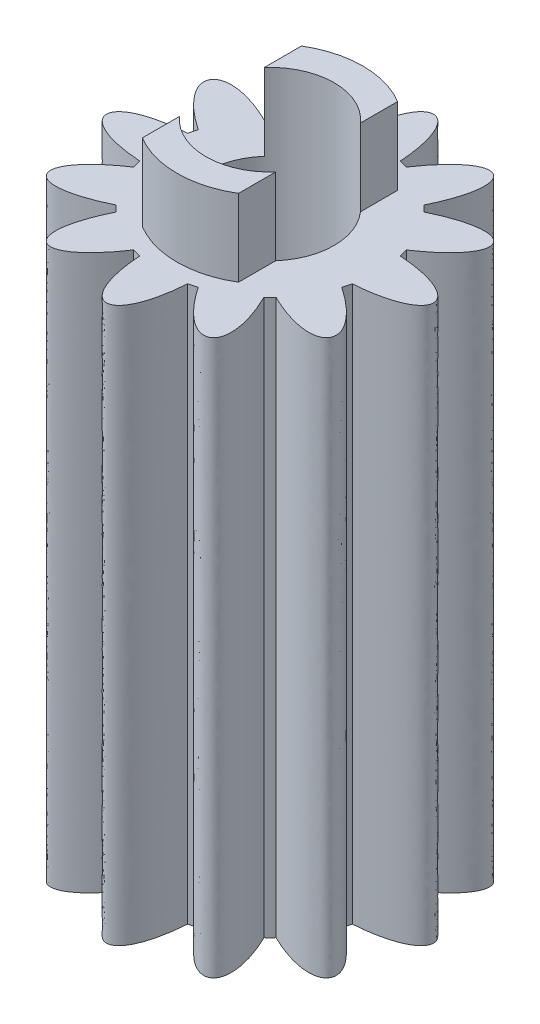
SolidWorks part; units mm, degrees
ref_plane "Front Plane" through (0, 0, 0) normal (0, 0, 1) x (1, 0, 0)
ref_plane "Top Plane" through (0, 0, 0) normal (0, 1, 0) x (1, 0, 0)
ref_plane "Right Plane" through (0, 0, 0) normal (1, 0, 0) x (0, 0, -1)
sketch "Sketch1" plane through (0, 0, 0) normal (0, 1, 0) x (1, 0, 0)
  line L0 (0, 0.0596) -> (0, 50000.0596) construction
  line L1 (0.75, -3.3162) -> (-0.75, -3.3162) construction
  line L2 (0.75, -3.3162) -> (0.75, 3.3162) construction
  line L3 (0.75, 3.3162) -> (-0.75, 3.3162) construction
  line L4 (-0.75, -3.3162) -> (-0.75, 3.3162) construction
  line L5 (0.75, -3.3162) -> (-0.75, 3.3162) construction
  line L6 (0.75, 3.3162) -> (-0.75, -3.3162) construction
  line L7 (0, 0) -> (0.75, 3.3162) construction
  circle A0 centre (0, 0) radius 3.4
  circle A1 centre (0, 0) radius 5.1 construction
  spline S0 degree 3 poles (-0.75, 3.3162) (-0.5833, 5.6946) (0.5833, 5.6946) (0.75, 3.3162) knots 0 0 0 0 1 1 1 1
  spline S1 degree 3 poles (1.0086, 3.247) (2.3421, 5.2233) (3.3525, 4.64) (2.3076, 2.497) knots 0 0 0 0 1 1 1 1
  spline S2 degree 3 poles (2.497, 2.3076) (4.64, 3.3525) (5.2233, 2.3421) (3.247, 1.0086) knots 0 0 0 0 1 1 1 1
  spline S3 degree 3 poles (3.3162, 0.75) (5.6946, 0.5833) (5.6946, -0.5833) (3.3162, -0.75) knots 0 0 0 0 1 1 1 1
  spline S4 degree 3 poles (3.247, -1.0086) (5.2233, -2.3421) (4.64, -3.3525) (2.497, -2.3076) knots 0 0 0 0 1 1 1 1
  spline S5 degree 3 poles (2.3076, -2.497) (3.3525, -4.64) (2.3421, -5.2233) (1.0086, -3.247) knots 0 0 0 0 1 1 1 1
  spline S6 degree 3 poles (0.75, -3.3162) (0.5833, -5.6946) (-0.5833, -5.6946) (-0.75, -3.3162) knots 0 0 0 0 1 1 1 1
  spline S7 degree 3 poles (-1.0086, -3.247) (-2.3421, -5.2233) (-3.3525, -4.64) (-2.3076, -2.497) knots 0 0 0 0 1 1 1 1
  spline S8 degree 3 poles (-2.497, -2.3076) (-4.64, -3.3525) (-5.2233, -2.3421) (-3.247, -1.0086) knots 0 0 0 0 1 1 1 1
  spline S9 degree 3 poles (-3.3162, -0.75) (-5.6946, -0.5833) (-5.6946, 0.5833) (-3.3162, 0.75) knots 0 0 0 0 1 1 1 1
  spline S10 degree 3 poles (-3.247, 1.0086) (-5.2233, 2.3421) (-4.64, 3.3525) (-2.497, 2.3076) knots 0 0 0 0 1 1 1 1
  spline S11 degree 3 poles (-2.3076, 2.497) (-3.3525, 4.64) (-2.3421, 5.2233) (-1.0086, 3.247) knots 0 0 0 0 1 1 1 1
  point P12 (0, 0)
  point P13 (0, 0)
  point P48 (0, 0)
  point P49 (0, 0)
  dimension "D1" = 6.8
  dimension "D2" = 10.2
  dimension "D3" = 1.5
  dimension "D4" = 3.4
extrude "Boss-Extrude1" add sketch "Sketch1" along normal blind 17.3 contours A0 | S9 A0 | S8 A0 | S7 A0 | S6 A0 | S5 A0 | S4 A0 | S3 A0 | S2 A0 | S1 A0 | S10 A0 | S11 A0 | S0 A0
sketch "Sketch4" plane through (0, 17.3, 0) normal (0, 1, 0) x (1, 0, 0)
  circle A0 centre (0, 0) radius 2.9
  dimension "D1" = 5.8
extrude "Boss-Extrude2" add sketch "Sketch4" along normal blind 2.4
sketch "Sketch2" plane through (0, 0, 0) normal (0, -1, 0) x (1, 0, 0)
  circle A0 centre (0, 0) radius 2
  dimension "D1" = 4
extrude "Cut-Extrude2" cut sketch "Sketch2" against normal blind 19.7
sketch "Sketch5" plane through (0, 17.3, 0) normal (0, 1, 0) x (1, 0, 0)
  line L1 (1.5, -6) -> (-1.5, -6) construction
  line L2 (1.5, -6) -> (1.5, 6) construction
  line L3 (1.5, 6) -> (-1.5, 6) construction
  line L4 (-1.5, -6) -> (-1.5, 6) construction
  line L5 (1.5, -6) -> (-1.5, 6) construction
  line L6 (1.5, 6) -> (-1.5, -6) construction
  line L7 (1.5, 6) -> (3.5, 6)
  line L8 (1.5, 6) -> (1.5, -6)
  line L9 (1.5, -6) -> (3.5, -6)
  line L10 (3.5, 6) -> (3.5, -6)
  line L11 (-1.5, 6) -> (-3.5, 6)
  line L12 (-1.5, 6) -> (-1.5, -6)
  line L13 (-1.5, -6) -> (-3.5, -6)
  line L14 (-3.5, 6) -> (-3.5, -6)
  point P0 (0, 0)
  dimension "D1" = 3
  dimension "D2" = 12
  dimension "D3" = 2
extrude "Cut-Extrude3" cut sketch "Sketch5" along normal blind 2.4
